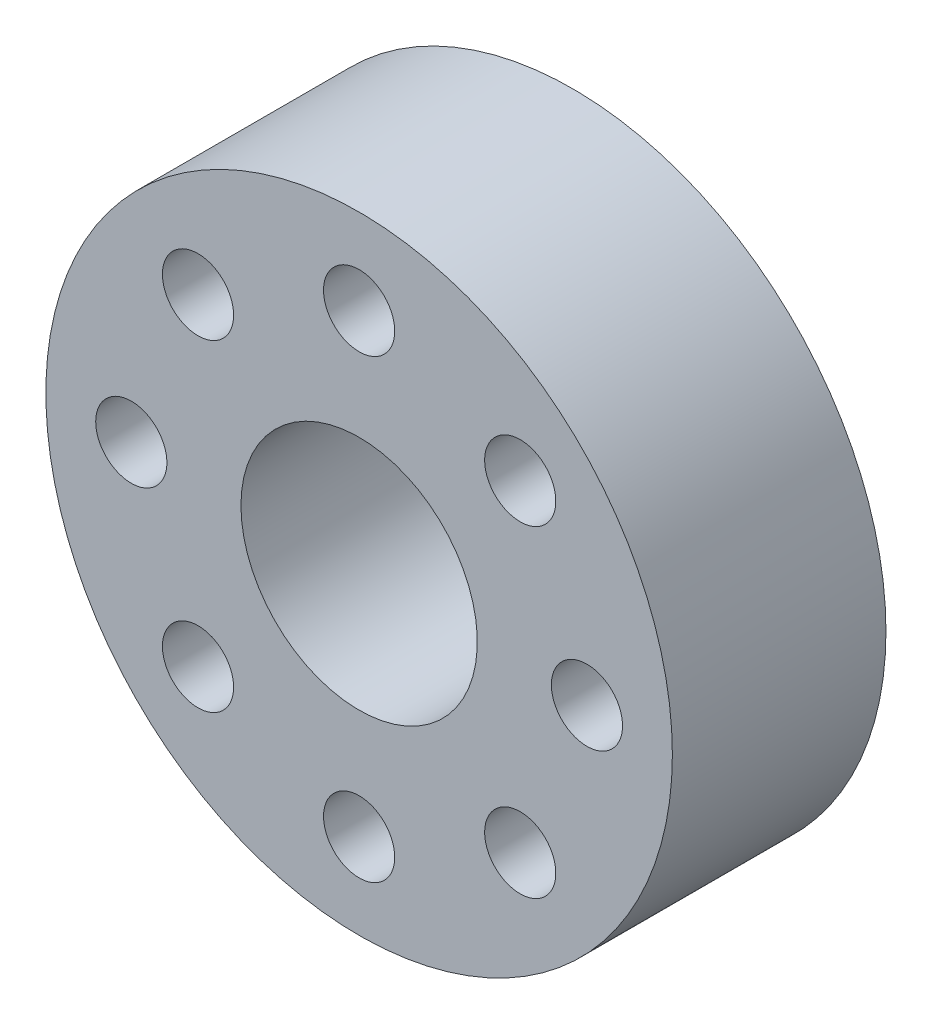
SolidWorks part; units mm, degrees
ref_plane "Front Plane" through (0, 0, 0) normal (0, 0, 1) x (1, 0, 0)
ref_plane "Top Plane" through (0, 0, 0) normal (0, 1, 0) x (1, 0, 0)
ref_plane "Right Plane" through (0, 0, 0) normal (1, 0, 0) x (0, 0, -1)
sketch "Sketch2" plane through (0, 0, 0) normal (0, 0, 1) x (1, 0, 0)
  circle A0 centre (0, 0) radius 11
  dimension "D1" = 22
extrude "Boss-Extrude1" add sketch "Sketch2" along normal blind 7.5
sketch "Sketch3" plane through (0, 0, 0) normal (0, 0, -1) x (-1, 0, 0)
  circle A0 centre (0, 0) radius 4.15
  circle A1 centre (8, 0) radius 1.25
  circle A2 centre (5.6569, -5.6569) radius 1.25
  circle A3 centre (0, -8) radius 1.25
  circle A4 centre (-5.6569, -5.6569) radius 1.25
  circle A5 centre (-8, 0) radius 1.25
  circle A6 centre (-5.6569, 5.6569) radius 1.25
  circle A7 centre (0, 8) radius 1.25
  circle A8 centre (5.6569, 5.6569) radius 1.25
  point P22 (0, 0)
  dimension "D1" = 8.3
  dimension "D3" = 2.5
  dimension "D2" = 8
  dimension "D4" = 8
extrude "Cut-Extrude1" cut sketch "Sketch3" against normal through all
